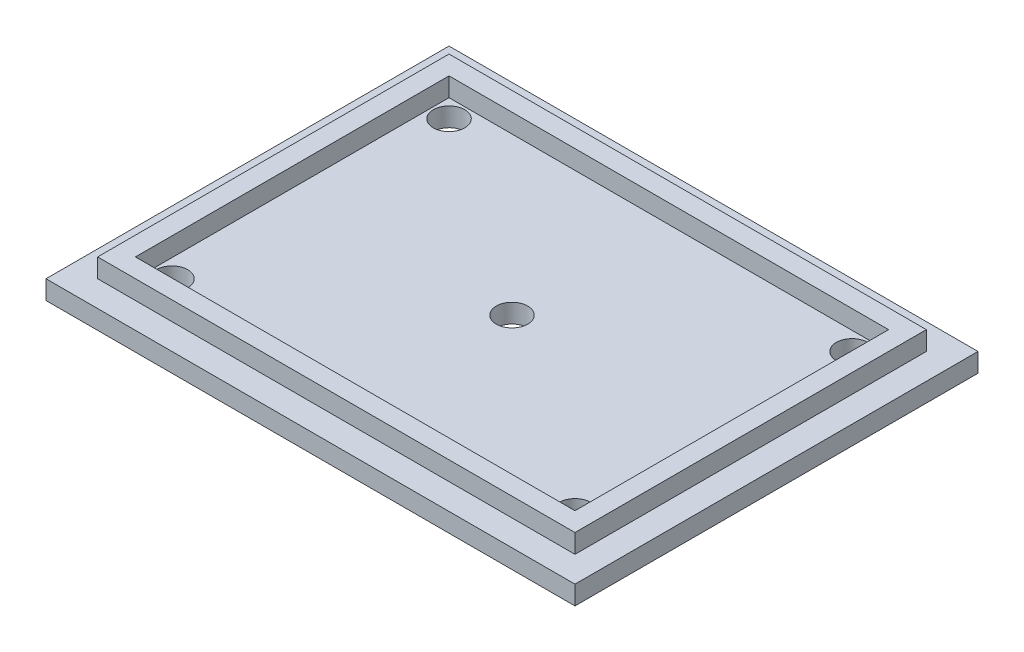
SolidWorks part; units mm, degrees
ref_plane "Front Plane" through (0, 0, 0) normal (0, 0, 1) x (1, 0, 0)
ref_plane "Top Plane" through (0, 0, 0) normal (0, 1, 0) x (1, 0, 0)
ref_plane "Right Plane" through (0, 0, 0) normal (1, 0, 0) x (0, 0, -1)
sketch "Croquis1" plane through (0, 0, 0) normal (0, 1, 0) x (1, 0, 0)
  line L1 (0, 0) -> (84, 0)
  line L2 (0, 0) -> (0, 64)
  line L3 (0, 64) -> (84, 64)
  line L4 (84, 0) -> (84, 64)
  dimension "D1" = 84
  dimension "D2" = 64
extrude "Saliente-Extruir1" add sketch "Croquis1" along normal blind 3
sketch "Croquis2" plane through (0, 3, 0) normal (0, 1, 0) x (1, 0, 0)
  line L0 (0, 64) -> (0, 0) construction
  line L1 (4.1, 59.9) -> (79.9, 59.9)
  line L2 (4.1, 59.9) -> (4.1, 4.1)
  line L3 (4.1, 4.1) -> (79.9, 4.1)
  line L4 (79.9, 59.9) -> (79.9, 4.1)
  line L5 (0, 0) -> (84, 0) construction
  line L6 (84, 64) -> (0, 64) construction
  line L7 (84, 0) -> (84, 64) construction
  line L8 (7.1, 56.9) -> (7.1, 7.1)
  line L9 (7.1, 7.1) -> (76.9, 7.1)
  line L10 (76.9, 56.9) -> (76.9, 7.1)
  line L11 (7.1, 56.9) -> (76.9, 56.9)
  dimension "D1" = 4.1
  dimension "D2" = 4.1
  dimension "D3" = 4.1
  dimension "D4" = 4.1
  dimension "D5" = 3
extrude "Saliente-Extruir2" add sketch "Croquis2" along normal blind 3
sketch "Croquis3" plane through (0, 0, 0) normal (0, -1, 0) x (1, 0, 0)
  line L0 (84, -64) -> (0, -64) construction
  line L1 (0, 0) -> (42, 0) construction
  line L2 (0, 0) -> (0, -64) construction
  line L3 (0, -64) -> (42, -64) construction
  line L6 (10, -10) -> (10, -54) construction
  line L7 (0, 0) -> (84, 0) construction
  line L8 (0, 0) -> (0, -64) construction
  line L9 (0, -64) -> (84, -64) construction
  line L10 (84, 0) -> (84, -64) construction
  line L11 (10, -54) -> (74, -54) construction
  line L12 (74, -10) -> (74, -54) construction
  line L13 (10, -10) -> (74, -10) construction
  circle A0 centre (42, -32) radius 2.5
  circle A1 centre (10, -10) radius 2.5
  circle A2 centre (74, -10) radius 2.5
  circle A3 centre (74, -54) radius 2.5
  circle A4 centre (10, -54) radius 2.5
  dimension "D1" = 5
  dimension "D3" = 5
  dimension "D2" = 10
  dimension "D4" = 2
  dimension "D5" = 2
extrude "Cortar-Extruir1" cut sketch "Croquis3" against normal through all
